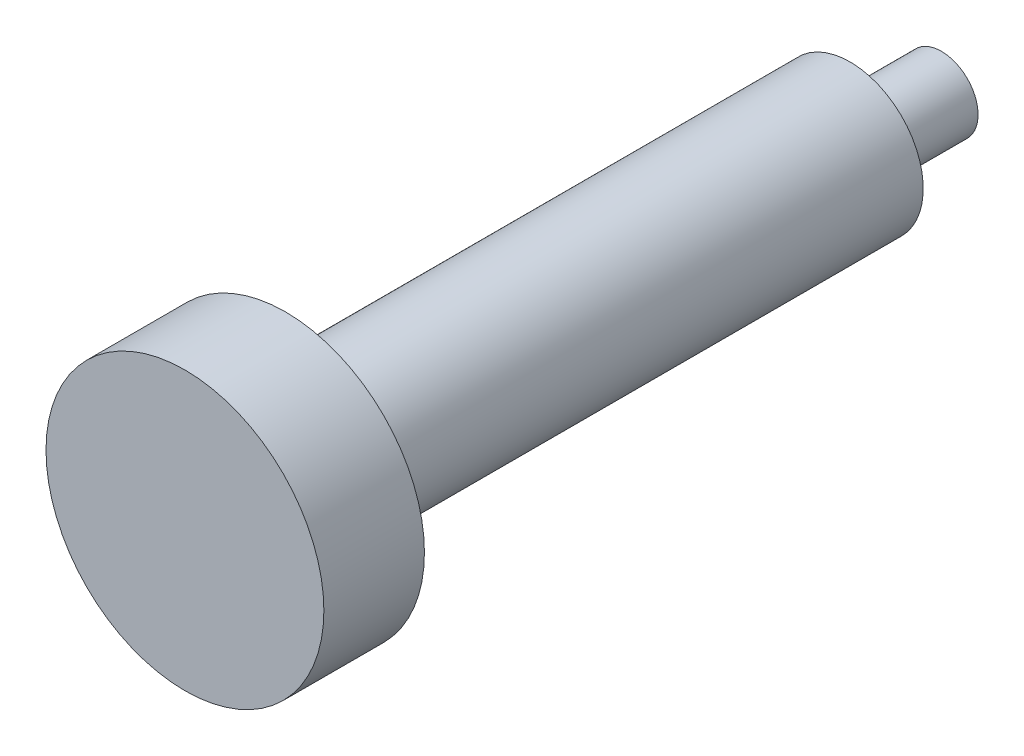
SolidWorks part; units mm, degrees
ref_plane "Ebene vorne" through (0, 0, 0) normal (0, 0, 1) x (1, 0, 0)
ref_plane "Ebene oben" through (0, 0, 0) normal (0, 1, 0) x (1, 0, 0)
ref_plane "Ebene rechts" through (0, 0, 0) normal (1, 0, 0) x (0, 0, -1)
curve "Kurve1"
  spline degree 3 poles (15.998, 0.279, 15.125) (15.9956, 0.372, 15.125) (15.9908, 0.5581, 15.125) (15.9788, 0.8371, 15.125) (15.9618, 1.1158, 15.125) (15.9399, 1.3942, 15.125) (15.9124, 1.6722, 15.125) (15.8823, 1.9501, 15.125) (15.8445, 2.2269, 15.125) (15.804, 2.5031, 15.125) (15.7577, 2.7784, 15.125) (15.7069, 3.0532, 15.125) (15.6507, 3.3268, 15.125) (15.5907, 3.5995, 15.125) (15.5259, 3.871, 15.125) (15.4558, 4.1413, 15.125) (15.3805, 4.4102, 15.125) (15.302, 4.6781, 15.125) (15.2177, 4.9445, 15.125) (15.1287, 5.209, 15.125) (15.0358, 5.4726, 15.125) (14.9376, 5.7341, 15.125) (14.836, 5.9944, 15.125) (14.7286, 6.2521, 15.125) (14.6179, 6.5085, 15.125) (14.5016, 6.7622, 15.125) (14.3819, 7.0146, 15.1251) (14.2566, 7.2643, 15.1247) (14.1278, 7.5122, 15.126) (13.9949, 7.7575, 15.1214) (13.8551, 8.0023, 15.1384) (13.7158, 8.2418, 15.0743) (13.5715, 8.4766, 15.0145) (13.4119, 8.7261, 15.0185) (13.2668, 8.9464, 14.8681) (13.1064, 9.1771, 14.7547) (12.936, 9.4181, 14.6379) (12.7787, 9.6289, 14.4401) (12.5998, 9.8636, 14.2514) (12.4267, 10.0781, 13.9999) (12.2726, 10.2687, 13.7104) (12.058, 10.5174, 13.4954) (11.9048, 10.6904, 13.1908) (11.6957, 10.9206, 12.9578) (11.5109, 11.1135, 12.6897) (11.3198, 11.3099, 12.4304) (11.1162, 11.5085, 12.1963) (10.9182, 11.6978, 11.969) (10.7057, 11.8912, 11.7712) (10.4991, 12.0738, 11.5699) (10.2899, 12.2548, 11.3786) (10.0702, 12.4333, 11.2113) (9.856, 12.6056, 11.046) (9.6251, 12.7816, 10.9139) (9.4039, 12.9462, 10.7491) (9.1806, 13.1038, 10.5834) (8.9611, 13.2571, 10.4164) (8.706, 13.4249, 10.3831) (8.4885, 13.564, 10.2365) (8.2385, 13.7179, 10.2093) (8.0015, 13.8555, 10.1253) (7.7559, 13.9958, 10.0697) (7.5146, 14.1265, 9.9855) (7.2658, 14.2558, 9.9304) (7.0136, 14.3823, 9.9041) (6.7627, 14.5013, 9.853) (6.509, 14.6177, 9.8142) (6.2527, 14.7284, 9.7808) (5.9938, 14.8362, 9.7728) (5.7346, 14.9374, 9.7179) (5.4729, 15.0357, 9.7656) (5.2088, 15.1288, 9.7494) (4.9445, 15.2177, 9.7668) (4.6756, 15.3028, 9.7735) (4.4132, 15.3797, 9.8501) (4.138, 15.4568, 9.8352) (3.8719, 15.5257, 9.9101) (3.5994, 15.5908, 9.9547) (3.3222, 15.6517, 10.0015) (3.0574, 15.7061, 10.1036) (2.7769, 15.758, 10.1515) (2.4995, 15.8045, 10.2212) (2.2248, 15.8448, 10.3192) (1.9478, 15.8826, 10.4276) (1.6757, 15.9121, 10.5538) (1.3922, 15.9401, 10.6531) (1.1115, 15.9621, 10.7671) (0.8378, 15.9789, 10.9076) (0.5476, 15.9908, 11.0382) (0.2878, 15.9992, 11.2279) (-0.0159, 16.0003, 11.3649) (-0.2625, 15.9997, 11.5869) (-0.586, 15.9894, 11.7221) (-0.8156, 15.98, 11.9867) (-1.1413, 15.9601, 12.1562) (-1.3812, 15.941, 12.4304) (-1.6762, 15.9121, 12.6534) (-1.9564, 15.8814, 12.8946) (-2.2189, 15.8456, 13.1573) (-2.5164, 15.8019, 13.3938) (-2.7761, 15.7581, 13.6775) (-3.0552, 15.7065, 13.9546) (-3.3276, 15.6505, 14.2408) (-3.6042, 15.5896, 14.5305) (-3.8666, 15.527, 14.8358) (-4.15, 15.4535, 15.1301) (-4.4027, 15.3826, 15.4504) (-4.6815, 15.301, 15.7484) (-4.9388, 15.2196, 16.0556) (-5.2143, 15.1269, 16.3448) (-5.4717, 15.0361, 16.6509) (-5.7331, 14.938, 16.9543) (-5.9942, 14.836, 17.2552) (-6.2531, 14.7281, 17.554) (-6.5023, 14.6207, 17.855) (-6.7639, 14.5007, 18.1312) (-6.9996, 14.3892, 18.4135) (-7.282, 14.2476, 18.6348) (-7.493, 14.138, 18.9244) (-7.766, 13.9903, 19.1354) (-7.9927, 13.8605, 19.3819) (-8.2391, 13.7175, 19.5942) (-8.476, 13.5718, 19.7935) (-8.7049, 13.4256, 19.9804) (-8.948, 13.2658, 20.1081) (-9.1746, 13.108, 20.2416) (-9.4022, 12.9475, 20.3582) (-9.6265, 12.7805, 20.4464) (-9.8488, 12.6112, 20.5201) (-10.0695, 12.4339, 20.501) (-10.2859, 12.2581, 20.5059) (-10.4973, 12.0754, 20.5054) (-10.7062, 11.8906, 20.5024) (-10.9142, 11.7015, 20.5151) (-11.1162, 11.5085, 20.4665) (-11.3163, 11.3133, 20.4075) (-11.5136, 11.1109, 20.3296) (-11.7057, 10.9097, 20.213) (-11.8883, 10.7089, 20.0701) (-12.0862, 10.4851, 19.9536) (-12.2576, 10.2864, 19.7502) (-12.4416, 10.06, 19.5571) (-12.6114, 9.8485, 19.3123) (-12.7811, 9.6258, 19.0534) (-12.9509, 9.3975, 18.7743) (-13.0975, 9.1894, 18.4671) (-13.2627, 8.9528, 18.2048) (-13.4265, 8.7036, 17.9675) (-13.5612, 8.4929, 17.6888) (-13.7144, 8.2445, 17.4654) (-13.8596, 7.9945, 17.2566) (-13.992, 7.7627, 17.0245) (-14.1253, 7.517, 16.8138) (-14.2569, 7.2636, 16.6283) (-14.3764, 7.0258, 16.4334) (-14.5034, 6.7583, 16.3047) (-14.6163, 6.5122, 16.1473) (-14.7275, 6.2547, 16.0139) (-14.8353, 5.9959, 15.8943) (-14.9368, 5.7363, 15.7837) (-15.0346, 5.4759, 15.6862) (-15.1284, 5.21, 15.6171) (-15.2193, 4.9397, 15.5658) (-15.2997, 4.6858, 15.4471) (-15.3813, 4.4076, 15.4409) (-15.4551, 4.1439, 15.3692) (-15.5264, 3.8691, 15.3634) (-15.5905, 3.6005, 15.3066) (-15.6506, 3.3275, 15.2711) (-15.707, 3.0528, 15.2592) (-15.7576, 2.7791, 15.2222) (-15.804, 2.503, 15.2321) (-15.8445, 2.227, 15.2294) (-15.8823, 1.9501, 15.2301) (-15.9124, 1.6722, 15.23) (-15.9399, 1.3942, 15.23) (-15.9618, 1.1158, 15.23) (-15.9789, 0.8371, 15.23) (-15.9904, 0.5581, 15.23) (-15.9993, 0.2791, 15.23) (-16.0003, 0, 15.23) (-15.9993, -0.2791, 15.23) (-15.9904, -0.5581, 15.23) (-15.9789, -0.8371, 15.23) (-15.9618, -1.1158, 15.23) (-15.9399, -1.3942, 15.23) (-15.9124, -1.6722, 15.23) (-15.8823, -1.9501, 15.23) (-15.8445, -2.2269, 15.23) (-15.804, -2.5031, 15.23) (-15.7577, -2.7784, 15.23) (-15.7069, -3.0532, 15.23) (-15.6507, -3.3268, 15.23) (-15.5907, -3.5995, 15.23) (-15.5259, -3.871, 15.23) (-15.4558, -4.1413, 15.23) (-15.3805, -4.4102, 15.23) (-15.302, -4.6781, 15.23) (-15.2177, -4.9445, 15.23) (-15.1287, -5.209, 15.23) (-15.0358, -5.4726, 15.23) (-14.9376, -5.7341, 15.23) (-14.836, -5.9944, 15.23) (-14.7286, -6.2521, 15.23) (-14.6179, -6.5085, 15.23) (-14.5016, -6.7622, 15.23) (-14.3819, -7.0146, 15.23) (-14.2566, -7.2643, 15.23) (-14.1278, -7.5121, 15.23) (-13.9948, -7.7577, 15.23) (-13.8563, -8.0001, 15.23) (-13.716, -8.2416, 15.23) (-13.5698, -8.4793, 15.23) (-13.4194, -8.7145, 15.23) (-13.266, -8.9478, 15.23) (-13.1062, -9.1772, 15.23) (-12.9451, -9.4055, 15.23) (-12.7782, -9.6295, 15.23) (-12.6091, -9.8516, 15.23) (-12.4341, -10.0692, 15.23) (-12.258, -10.2859, 15.23) (-12.0755, -10.4973, 15.23) (-11.8905, -10.7064, 15.23) (-11.7026, -10.9131, 15.23) (-11.5097, -11.115, 15.23) (-11.3148, -11.3148, 15.23) (-11.115, -11.5097, 15.23) (-10.9131, -11.7026, 15.23) (-10.7064, -11.8905, 15.23) (-10.4973, -12.0755, 15.23) (-10.2859, -12.258, 15.23) (-10.0692, -12.4341, 15.23) (-9.8516, -12.6091, 15.23) (-9.6295, -12.7782, 15.23) (-9.4055, -12.9451, 15.23) (-9.1772, -13.1062, 15.23) (-8.9478, -13.266, 15.23) (-8.7145, -13.4194, 15.23) (-8.4793, -13.5698, 15.23) (-8.2416, -13.716, 15.23) (-8.0001, -13.8563, 15.23) (-7.7577, -13.9948, 15.23) (-7.5121, -14.1278, 15.23) (-7.2643, -14.2566, 15.23) (-7.0146, -14.3819, 15.23) (-6.7622, -14.5016, 15.23) (-6.5085, -14.6179, 15.23) (-6.2521, -14.7286, 15.23) (-5.9944, -14.836, 15.23) (-5.7341, -14.9376, 15.23) (-5.4726, -15.0358, 15.23) (-5.209, -15.1287, 15.23) (-4.9445, -15.2177, 15.23) (-4.6781, -15.302, 15.23) (-4.4102, -15.3805, 15.23) (-4.1413, -15.4558, 15.23) (-3.871, -15.5259, 15.23) (-3.5995, -15.5907, 15.23) (-3.3268, -15.6507, 15.23) (-3.0532, -15.7069, 15.23) (-2.7784, -15.7577, 15.23) (-2.5031, -15.804, 15.23) (-2.2269, -15.8445, 15.23) (-1.9501, -15.8823, 15.23) (-1.6722, -15.9124, 15.23) (-1.3942, -15.9399, 15.23) (-1.1158, -15.9618, 15.23) (-0.8371, -15.9789, 15.23) (-0.5581, -15.9904, 15.23) (-0.2791, -15.9993, 15.23) (0, -16.0003, 15.23) (0.2791, -15.9993, 15.23) (0.5581, -15.9904, 15.23) (0.8371, -15.9789, 15.23) (1.1158, -15.9618, 15.23) (1.3942, -15.9399, 15.23) (1.6722, -15.9124, 15.23) (1.9501, -15.8823, 15.23) (2.2269, -15.8445, 15.23) (2.5031, -15.804, 15.23) (2.7784, -15.7577, 15.23) (3.0532, -15.7069, 15.23) (3.3268, -15.6507, 15.23) (3.5995, -15.5907, 15.23) (3.871, -15.5259, 15.23) (4.1413, -15.4558, 15.23) (4.4102, -15.3805, 15.23) (4.6781, -15.302, 15.23) (4.9445, -15.2177, 15.23) (5.209, -15.1287, 15.23) (5.4726, -15.0358, 15.23) (5.7341, -14.9376, 15.23) (5.9944, -14.836, 15.23) (6.2521, -14.7286, 15.23) (6.5085, -14.6179, 15.23) (6.7622, -14.5016, 15.23) (7.0146, -14.3819, 15.23) (7.2643, -14.2566, 15.23) (7.5121, -14.1278, 15.23) (7.7577, -13.9948, 15.23) (8.0001, -13.8563, 15.23) (8.2416, -13.716, 15.23) (8.4793, -13.5698, 15.23) (8.7145, -13.4194, 15.23) (8.9478, -13.266, 15.23) (9.1772, -13.1062, 15.23) (9.4055, -12.9451, 15.23) (9.6295, -12.7782, 15.23) (9.8516, -12.6091, 15.23) (10.0692, -12.4341, 15.23) (10.2859, -12.258, 15.23) (10.4973, -12.0755, 15.23) (10.7064, -11.8905, 15.23) (10.9131, -11.7026, 15.23) (11.115, -11.5097, 15.23) (11.3148, -11.3148, 15.23) (11.5097, -11.115, 15.23) (11.7025, -10.9131, 15.23) (11.8906, -10.7065, 15.23) (12.0135, -10.5668, 15.23) (12.075, -10.497, 15.23) knots 0 0 0 0 0.002912 0.005826 0.008742 0.011651 0.014566 0.017484 0.0204 0.023311 0.02622 0.029138 0.032056 0.034962 0.03788 0.04079 0.043703 0.046618 0.049529 0.052445 0.055356 0.058274 0.061188 0.064102 0.067014 0.069927 0.072839 0.075755 0.078672 0.08158 0.084496 0.087455 0.090415 0.09334 0.096512 0.099686 0.102883 0.106374 0.10993 0.113838 0.118001 0.121744 0.125981 0.12982 0.133843 0.137819 0.141622 0.14537 0.148951 0.152534 0.156059 0.15947 0.162825 0.166087 0.169441 0.172856 0.176142 0.179146 0.182273 0.185242 0.188246 0.191239 0.194251 0.197223 0.200162 0.203112 0.206055 0.208983 0.211905 0.214835 0.217761 0.220672 0.22359 0.226508 0.22947 0.232387 0.235353 0.238318 0.24128 0.244329 0.247314 0.250313 0.253388 0.256522 0.259697 0.262811 0.265958 0.269197 0.272456 0.275893 0.279223 0.282804 0.286161 0.290003 0.293529 0.297507 0.301282 0.305127 0.30911 0.31295 0.317072 0.321202 0.325367 0.329563 0.33388 0.338116 0.342547 0.346824 0.351137 0.355339 0.359652 0.363969 0.368246 0.372522 0.376797 0.380923 0.385011 0.388787 0.392915 0.39662 0.400464 0.40414 0.407724 0.411186 0.414423 0.41764 0.420795 0.423852 0.426835 0.429745 0.432659 0.435574 0.438486 0.441396 0.444348 0.447322 0.450346 0.453505 0.456738 0.45995 0.463475 0.467059 0.470898 0.474882 0.479004 0.483361 0.487344 0.491186 0.495272 0.499013 0.502658 0.506434 0.510076 0.513602 0.517099 0.520357 0.523664 0.526898 0.53007 0.533202 0.536284 0.539285 0.542279 0.545337 0.548275 0.551235 0.554157 0.557112 0.560041 0.562966 0.565896 0.568805 0.571716 0.574632 0.57755 0.580464 0.583374 0.58629 0.589204 0.592116 0.595027 0.597938 0.60085 0.603764 0.60668 0.609589 0.612503 0.615422 0.618338 0.621249 0.624158 0.627076 0.629994 0.6329 0.635818 0.638728 0.641641 0.644556 0.647467 0.650383 0.653294 0.656212 0.659126 0.66204 0.664951 0.667865 0.670777 0.673693 0.67661 0.679518 0.682434 0.685347 0.68826 0.691169 0.694083 0.697 0.699918 0.702827 0.705744 0.708654 0.711568 0.714483 0.717395 0.720305 0.723227 0.726134 0.729041 0.731964 0.734873 0.737785 0.7407 0.743614 0.746524 0.749442 0.75235 0.755268 0.758186 0.7611 0.764008 0.766922 0.769835 0.77275 0.775659 0.778575 0.781492 0.784404 0.787317 0.790228 0.793142 0.796056 0.798975 0.801885 0.804802 0.807712 0.810627 0.813541 0.816451 0.819369 0.822275 0.825193 0.828111 0.83102 0.833931 0.836847 0.839765 0.842679 0.845589 0.848505 0.851418 0.854331 0.857242 0.860153 0.863065 0.865978 0.868894 0.871804 0.874718 0.877637 0.880552 0.883463 0.886372 0.889291 0.892208 0.895114 0.898032 0.900942 0.903856 0.906771 0.909681 0.912598 0.915508 0.918427 0.921341 0.924255 0.927166 0.930079 0.932992 0.935908 0.938824 0.941733 0.944648 0.947562 0.950475 0.953383 0.956297 0.959215 0.962133 0.965042 0.967959 0.970869 0.973783 0.976698 0.97961 0.98252 0.985442 0.988349 0.991256 0.994178 0.997088 1 1 1 1
curve "Kurve2"
  spline degree 3 poles (15.998, 0.279, 58.63) (15.9956, 0.372, 58.63) (15.9908, 0.5581, 58.63) (15.9788, 0.8371, 58.63) (15.9618, 1.1158, 58.63) (15.9399, 1.3942, 58.63) (15.9124, 1.6722, 58.63) (15.8823, 1.9501, 58.63) (15.8445, 2.2269, 58.63) (15.804, 2.5031, 58.63) (15.7577, 2.7784, 58.63) (15.7069, 3.0532, 58.63) (15.6507, 3.3268, 58.63) (15.5907, 3.5995, 58.63) (15.5259, 3.871, 58.63) (15.4558, 4.1413, 58.63) (15.3805, 4.4102, 58.63) (15.302, 4.6781, 58.63) (15.2177, 4.9445, 58.63) (15.1287, 5.209, 58.63) (15.0358, 5.4726, 58.63) (14.9376, 5.7341, 58.63) (14.836, 5.9944, 58.63) (14.7286, 6.2521, 58.63) (14.6179, 6.5085, 58.63) (14.5016, 6.7622, 58.63) (14.3819, 7.0146, 58.63) (14.2566, 7.2643, 58.63) (14.1278, 7.5121, 58.63) (13.9948, 7.7577, 58.63) (13.8563, 8.0001, 58.63) (13.716, 8.2416, 58.63) (13.5698, 8.4793, 58.63) (13.4194, 8.7145, 58.63) (13.266, 8.9478, 58.63) (13.1062, 9.1772, 58.63) (12.9451, 9.4055, 58.63) (12.7782, 9.6295, 58.63) (12.6091, 9.8516, 58.63) (12.4341, 10.0692, 58.63) (12.258, 10.2859, 58.63) (12.0755, 10.4973, 58.63) (11.8905, 10.7064, 58.63) (11.7026, 10.9131, 58.63) (11.5097, 11.115, 58.63) (11.3148, 11.3148, 58.63) (11.115, 11.5097, 58.63) (10.9131, 11.7026, 58.63) (10.7064, 11.8905, 58.63) (10.4973, 12.0755, 58.63) (10.2859, 12.258, 58.63) (10.0692, 12.4341, 58.63) (9.8516, 12.6091, 58.63) (9.6295, 12.7782, 58.63) (9.4055, 12.9451, 58.63) (9.1772, 13.1062, 58.63) (8.9478, 13.266, 58.63) (8.7145, 13.4194, 58.63) (8.4793, 13.5698, 58.63) (8.2416, 13.716, 58.63) (8.0001, 13.8563, 58.63) (7.7577, 13.9948, 58.63) (7.5121, 14.1278, 58.63) (7.2643, 14.2566, 58.63) (7.0146, 14.3819, 58.63) (6.7622, 14.5016, 58.63) (6.5085, 14.6179, 58.63) (6.2521, 14.7286, 58.63) (5.9944, 14.836, 58.63) (5.7341, 14.9376, 58.63) (5.4726, 15.0358, 58.63) (5.209, 15.1287, 58.63) (4.9445, 15.2177, 58.63) (4.6781, 15.302, 58.63) (4.4102, 15.3805, 58.63) (4.1413, 15.4558, 58.63) (3.871, 15.5259, 58.63) (3.5995, 15.5907, 58.63) (3.3268, 15.6507, 58.63) (3.0532, 15.7069, 58.63) (2.7784, 15.7577, 58.63) (2.5031, 15.804, 58.63) (2.2269, 15.8445, 58.63) (1.9501, 15.8823, 58.63) (1.6722, 15.9124, 58.63) (1.3942, 15.9399, 58.63) (1.1158, 15.9618, 58.63) (0.8371, 15.9789, 58.63) (0.5581, 15.9904, 58.63) (0.2791, 15.9993, 58.63) (0, 16.0003, 58.63) (-0.2791, 15.9993, 58.63) (-0.5581, 15.9904, 58.63) (-0.8371, 15.9789, 58.63) (-1.1158, 15.9618, 58.63) (-1.3942, 15.9399, 58.63) (-1.6722, 15.9124, 58.63) (-1.9501, 15.8823, 58.63) (-2.2269, 15.8445, 58.63) (-2.5031, 15.804, 58.63) (-2.7784, 15.7577, 58.63) (-3.0532, 15.7069, 58.63) (-3.3268, 15.6507, 58.63) (-3.5995, 15.5907, 58.63) (-3.871, 15.5259, 58.63) (-4.1413, 15.4558, 58.63) (-4.4102, 15.3805, 58.63) (-4.6781, 15.302, 58.63) (-4.9445, 15.2177, 58.63) (-5.209, 15.1287, 58.63) (-5.4726, 15.0358, 58.63) (-5.7341, 14.9376, 58.63) (-5.9944, 14.836, 58.63) (-6.2521, 14.7286, 58.63) (-6.5085, 14.6179, 58.63) (-6.7622, 14.5016, 58.63) (-7.0146, 14.3819, 58.63) (-7.2643, 14.2566, 58.63) (-7.5121, 14.1278, 58.63) (-7.7577, 13.9948, 58.63) (-8.0001, 13.8563, 58.63) (-8.2416, 13.716, 58.63) (-8.4793, 13.5698, 58.63) (-8.7145, 13.4194, 58.63) (-8.9478, 13.266, 58.63) (-9.1772, 13.1062, 58.63) (-9.4055, 12.9451, 58.63) (-9.6295, 12.7782, 58.63) (-9.8516, 12.6091, 58.63) (-10.0692, 12.4341, 58.63) (-10.2859, 12.258, 58.63) (-10.4973, 12.0755, 58.63) (-10.7064, 11.8905, 58.63) (-10.9131, 11.7026, 58.63) (-11.115, 11.5097, 58.63) (-11.3148, 11.3148, 58.63) (-11.5097, 11.115, 58.63) (-11.7026, 10.9131, 58.63) (-11.8905, 10.7064, 58.63) (-12.0755, 10.4973, 58.63) (-12.258, 10.2859, 58.63) (-12.4341, 10.0692, 58.63) (-12.6091, 9.8516, 58.63) (-12.7782, 9.6295, 58.63) (-12.9451, 9.4055, 58.63) (-13.1062, 9.1772, 58.63) (-13.266, 8.9478, 58.63) (-13.4194, 8.7145, 58.63) (-13.5698, 8.4793, 58.63) (-13.716, 8.2416, 58.63) (-13.8563, 8.0001, 58.63) (-13.9948, 7.7577, 58.63) (-14.1278, 7.5121, 58.63) (-14.2566, 7.2643, 58.63) (-14.3819, 7.0146, 58.63) (-14.5016, 6.7622, 58.63) (-14.6179, 6.5085, 58.63) (-14.7286, 6.2521, 58.63) (-14.836, 5.9944, 58.63) (-14.9376, 5.7341, 58.63) (-15.0358, 5.4726, 58.63) (-15.1287, 5.209, 58.63) (-15.2177, 4.9445, 58.63) (-15.302, 4.6781, 58.63) (-15.3805, 4.4102, 58.63) (-15.4558, 4.1413, 58.63) (-15.5259, 3.871, 58.63) (-15.5907, 3.5995, 58.63) (-15.6507, 3.3268, 58.63) (-15.7069, 3.0532, 58.63) (-15.7577, 2.7784, 58.63) (-15.804, 2.5031, 58.63) (-15.8445, 2.2269, 58.63) (-15.8823, 1.9501, 58.63) (-15.9124, 1.6722, 58.63) (-15.9399, 1.3942, 58.63) (-15.9618, 1.1158, 58.63) (-15.9789, 0.8371, 58.63) (-15.9904, 0.5581, 58.63) (-15.9993, 0.2791, 58.63) (-16.0003, 0, 58.63) (-15.9993, -0.2791, 58.63) (-15.9904, -0.5581, 58.63) (-15.9789, -0.8371, 58.63) (-15.9618, -1.1158, 58.63) (-15.9399, -1.3942, 58.63) (-15.9124, -1.6722, 58.63) (-15.8823, -1.9501, 58.63) (-15.8445, -2.2269, 58.63) (-15.804, -2.5031, 58.63) (-15.7577, -2.7784, 58.63) (-15.7069, -3.0532, 58.63) (-15.6507, -3.3268, 58.63) (-15.5907, -3.5995, 58.63) (-15.5259, -3.871, 58.63) (-15.4558, -4.1413, 58.63) (-15.3805, -4.4102, 58.63) (-15.302, -4.6781, 58.63) (-15.2177, -4.9445, 58.63) (-15.1287, -5.209, 58.63) (-15.0358, -5.4726, 58.63) (-14.9376, -5.7341, 58.63) (-14.836, -5.9944, 58.63) (-14.7286, -6.2521, 58.63) (-14.6179, -6.5085, 58.6301) (-14.5016, -6.7622, 58.6298) (-14.3818, -7.0146, 58.6308) (-14.2567, -7.2641, 58.6271) (-14.1271, -7.5136, 58.6407) (-13.9945, -7.7583, 58.5895) (-13.8563, -8.0002, 58.5403) (-13.716, -8.2417, 58.489) (-13.5647, -8.4873, 58.4419) (-13.4193, -8.7147, 58.3115) (-13.2626, -8.9527, 58.194) (-13.1041, -9.1802, 58.0385) (-12.9343, -9.4203, 57.8699) (-12.7843, -9.6214, 57.624) (-12.6003, -9.8629, 57.4189) (-12.4377, -10.0647, 57.1567) (-12.2556, -10.2889, 56.9178) (-12.0823, -10.4894, 56.6626) (-11.8847, -10.7129, 56.4471) (-11.7036, -10.9118, 56.1999) (-11.5164, -11.1081, 55.958) (-11.3069, -11.3227, 55.7538) (-11.1226, -11.5023, 55.5069) (-10.9138, -11.702, 55.3019) (-10.709, -11.8881, 55.1001) (-10.5017, -12.0717, 54.9123) (-10.2819, -12.2614, 54.7535) (-10.0735, -12.4306, 54.5678) (-9.855, -12.6065, 54.4085) (-9.6301, -12.7778, 54.27) (-9.4058, -12.9449, 54.1359) (-9.1816, -13.1032, 53.9993) (-8.9418, -13.27, 53.9032) (-8.7215, -13.4148, 53.752) (-8.4799, -13.5694, 53.6608) (-8.2429, -13.7152, 53.5686) (-8.0014, -13.8556, 53.4875) (-7.7571, -13.9951, 53.4233) (-7.5155, -14.1261, 53.3405) (-7.2628, -14.2573, 53.3169) (-7.0166, -14.3809, 53.2517) (-6.7618, -14.5018, 53.2374) (-6.5081, -14.6181, 53.2088) (-6.2535, -14.728, 53.1574) (-5.9935, -14.8363, 53.1816) (-5.7349, -14.9373, 53.1359) (-5.4723, -15.0359, 53.1449) (-5.2083, -15.1289, 53.1543) (-4.9454, -15.2174, 53.198) (-4.6773, -15.3023, 53.1933) (-4.4095, -15.3807, 53.2289) (-4.1416, -15.4558, 53.2715) (-3.8693, -15.5263, 53.3051) (-3.6007, -15.5905, 53.3693) (-3.3233, -15.6514, 53.4076) (-3.0544, -15.7067, 53.4935) (-2.7776, -15.7579, 53.5583) (-2.5017, -15.8042, 53.6335) (-2.2259, -15.8446, 53.7198) (-1.9453, -15.8829, 53.8109) (-1.6719, -15.9124, 53.9346) (-1.3988, -15.9396, 54.0608) (-1.1033, -15.9627, 54.1494) (-0.8425, -15.9786, 54.3208) (-0.5566, -15.9905, 54.4536) (-0.2731, -15.9994, 54.5979) (0.002, -16.0003, 54.7702) (0.2797, -15.9993, 54.9506) (0.5635, -15.9902, 55.1339) (0.8388, -15.9789, 55.3411) (1.1194, -15.9615, 55.5538) (1.3909, -15.9402, 55.7825) (1.6827, -15.9113, 55.9974) (1.9411, -15.8834, 56.2538) (2.243, -15.8423, 56.4787) (2.5036, -15.8038, 56.7613) (2.7688, -15.7594, 57.0451) (3.0614, -15.7054, 57.3011) (3.3403, -15.6477, 57.5858) (3.5798, -15.5953, 57.9107) (3.8868, -15.5221, 58.1794) (4.141, -15.4558, 58.4971) (4.4045, -15.3822, 58.8136) (4.6803, -15.3013, 59.1146) (4.9442, -15.2178, 59.4202) (5.2065, -15.1295, 59.7241) (5.4722, -15.036, 60.0204) (5.7373, -14.9364, 60.3151) (5.9924, -14.8368, 60.6204) (6.2532, -14.7281, 60.9189) (6.5027, -14.6205, 61.2194) (6.7629, -14.5013, 61.4993) (7.013, -14.3826, 61.7783) (7.2537, -14.262, 62.0501) (7.5133, -14.1273, 62.2785) (7.7587, -13.9942, 62.5102) (7.9979, -13.8576, 62.7446) (8.2381, -13.7181, 62.9703) (8.4782, -13.5704, 63.1782) (8.7074, -13.424, 63.3829) (8.9474, -13.2663, 63.5474) (9.1687, -13.1121, 63.7156) (9.4029, -12.947, 63.8279) (9.6312, -12.777, 63.9146) (9.8458, -12.6136, 64.0332) (10.0728, -12.4312, 64.0659) (10.2802, -12.2628, 64.1843) (10.498, -12.0749, 64.1536) (10.7062, -11.8907, 64.1617) (10.9131, -11.7025, 64.1595) (11.115, -11.5097, 64.1601) (11.3148, -11.3148, 64.16) (11.5097, -11.115, 64.16) (11.7026, -10.9131, 64.16) (11.8904, -10.7063, 64.16) (12.0758, -10.4975, 64.16) (12.1966, -10.3559, 64.16) (12.257, -10.285, 64.16) knots 0 0 0 0 0.002952 0.005906 0.008862 0.011811 0.014765 0.017724 0.02068 0.023631 0.02658 0.029538 0.032496 0.035442 0.038399 0.041349 0.044303 0.047258 0.050208 0.053165 0.056115 0.059074 0.062028 0.064982 0.067933 0.070886 0.073838 0.076795 0.079751 0.0827 0.085655 0.088608 0.091561 0.09451 0.097464 0.100421 0.103379 0.106328 0.109286 0.112236 0.115189 0.118144 0.121096 0.124046 0.127009 0.129955 0.132902 0.135865 0.138814 0.141766 0.144721 0.147675 0.150625 0.153582 0.156531 0.159489 0.162447 0.1654 0.168349 0.171302 0.174255 0.177211 0.180159 0.183116 0.186072 0.189024 0.191977 0.194929 0.197883 0.200837 0.203795 0.206746 0.209702 0.212652 0.215607 0.218561 0.221511 0.224469 0.227415 0.230373 0.233331 0.23628 0.239231 0.242187 0.245145 0.248099 0.251049 0.254005 0.256958 0.259911 0.262861 0.265812 0.268764 0.271718 0.274674 0.277624 0.280578 0.283536 0.286492 0.289443 0.292392 0.29535 0.298308 0.301254 0.304212 0.307162 0.310115 0.31307 0.316021 0.318977 0.321928 0.324886 0.32784 0.330794 0.333745 0.336699 0.339651 0.342607 0.345564 0.348512 0.351468 0.354421 0.357374 0.360322 0.363276 0.366234 0.369192 0.372141 0.375098 0.378048 0.381002 0.383957 0.386909 0.389858 0.392821 0.395768 0.398714 0.401677 0.404627 0.407579 0.410534 0.413487 0.416437 0.419395 0.422343 0.425302 0.428259 0.431213 0.434161 0.437115 0.440068 0.443023 0.445972 0.448928 0.451884 0.454837 0.45779 0.460741 0.463695 0.466649 0.469607 0.472558 0.475514 0.478465 0.48142 0.484373 0.487323 0.490281 0.493227 0.496185 0.499143 0.502092 0.505043 0.507999 0.510957 0.513912 0.516861 0.519817 0.522771 0.525723 0.528674 0.531625 0.534577 0.53753 0.540487 0.543436 0.54639 0.549349 0.552304 0.555255 0.558204 0.561163 0.56412 0.567066 0.570024 0.572974 0.575928 0.578883 0.581833 0.58479 0.58774 0.590699 0.593653 0.596607 0.599558 0.602511 0.605463 0.608419 0.611376 0.614355 0.617357 0.620357 0.623378 0.626567 0.629804 0.63316 0.636649 0.640506 0.644236 0.648233 0.652162 0.656128 0.659886 0.663813 0.667714 0.671404 0.675293 0.678996 0.682626 0.686167 0.689599 0.693113 0.696514 0.699821 0.703098 0.70636 0.709538 0.712818 0.715951 0.719054 0.722126 0.725173 0.728213 0.731199 0.734202 0.737166 0.740137 0.743111 0.746065 0.749031 0.751989 0.754944 0.757917 0.76087 0.763842 0.766825 0.769806 0.77282 0.775813 0.778876 0.781925 0.784979 0.788064 0.791185 0.794405 0.79762 0.800771 0.804152 0.807456 0.810782 0.814238 0.81775 0.821291 0.824955 0.828685 0.832475 0.836235 0.840203 0.844031 0.848212 0.852429 0.856432 0.860655 0.865182 0.869293 0.873743 0.878235 0.882571 0.886943 0.891318 0.895613 0.899912 0.904286 0.908621 0.912955 0.917137 0.921318 0.925429 0.929257 0.93308 0.936941 0.940734 0.944429 0.948058 0.951516 0.954923 0.958122 0.961237 0.964378 0.967395 0.970468 0.973423 0.976375 0.979325 0.982287 0.985234 0.988181 0.991143 0.994093 0.997045 1 1 1 1
curve "Kurve3"
  spline degree 3 poles (15.998, 0.279, 106.17) (15.9956, 0.372, 106.17) (15.9908, 0.5581, 106.17) (15.9788, 0.8371, 106.17) (15.9618, 1.1158, 106.17) (15.9399, 1.3942, 106.17) (15.9124, 1.6722, 106.17) (15.8823, 1.9501, 106.17) (15.8445, 2.2269, 106.17) (15.804, 2.5031, 106.1701) (15.7577, 2.7784, 106.1697) (15.7069, 3.0533, 106.1713) (15.6508, 3.3263, 106.1653) (15.5899, 3.6032, 106.1878) (15.5267, 3.8681, 106.1022) (15.4544, 4.1469, 106.0941) (15.3803, 4.4108, 105.9973) (15.3012, 4.6807, 105.9132) (15.217, 4.9466, 105.8055) (15.1268, 5.2145, 105.6875) (15.0323, 5.4822, 105.5382) (14.9387, 5.7313, 105.3421) (14.834, 5.9994, 105.1612) (14.7257, 6.2587, 104.9557) (14.62, 6.5039, 104.7237) (14.5017, 6.762, 104.5097) (14.3788, 7.0207, 104.2969) (14.2603, 7.2571, 104.0566) (14.1218, 7.5236, 103.8472) (13.9948, 7.7575, 103.5898) (13.8628, 7.989, 103.333) (13.7112, 8.2497, 103.1232) (13.5722, 8.4753, 102.8777) (13.4177, 8.717, 102.652) (13.2708, 8.9406, 102.4142) (13.11, 9.1718, 102.2103) (12.9485, 9.4009, 102.032) (12.7734, 9.6359, 101.8851) (12.6138, 9.8455, 101.6956) (12.4335, 10.0701, 101.5464) (12.2595, 10.2841, 101.3918) (12.0833, 10.4884, 101.2377) (11.8872, 10.7101, 101.1752) (11.708, 10.9072, 101.0512) (11.5084, 11.1163, 101.0162) (11.3162, 11.3134, 100.9447) (11.1153, 11.5094, 100.9063) (10.9141, 11.7016, 100.8602) (10.7059, 11.891, 100.8732) (10.4977, 12.0751, 100.8367) (10.2858, 12.2582, 100.8498) (10.0693, 12.4341, 100.8339) (9.8516, 12.6091, 100.8246) (9.6294, 12.7783, 100.8175) (9.4057, 12.945, 100.7953) (9.1772, 13.1062, 100.8013) (8.9478, 13.266, 100.7997) (8.7145, 13.4194, 100.8001) (8.4793, 13.5698, 100.8) (8.2416, 13.716, 100.8) (8.0001, 13.8563, 100.8) (7.7577, 13.9948, 100.8) (7.5121, 14.1278, 100.8) (7.2643, 14.2566, 100.8) (7.0146, 14.3819, 100.8) (6.7622, 14.5016, 100.8) (6.5085, 14.6179, 100.8) (6.2521, 14.7286, 100.8) (5.9944, 14.836, 100.8) (5.7341, 14.9376, 100.8) (5.4726, 15.0358, 100.8) (5.209, 15.1287, 100.8) (4.9445, 15.2177, 100.8) (4.6781, 15.302, 100.8) (4.4102, 15.3805, 100.8) (4.1413, 15.4558, 100.8) (3.871, 15.5259, 100.8) (3.5995, 15.5907, 100.8) (3.3268, 15.6507, 100.8) (3.0532, 15.7069, 100.8) (2.7784, 15.7577, 100.8) (2.5031, 15.804, 100.8) (2.2269, 15.8445, 100.8) (1.9501, 15.8823, 100.8) (1.6722, 15.9124, 100.8) (1.3942, 15.9399, 100.8) (1.1158, 15.9618, 100.8) (0.8371, 15.9789, 100.8) (0.5581, 15.9904, 100.8) (0.2791, 15.9993, 100.8) (0, 16.0003, 100.8) (-0.2791, 15.9993, 100.8) (-0.5581, 15.9904, 100.8) (-0.8371, 15.9789, 100.8) (-1.1158, 15.9618, 100.8) (-1.3942, 15.9399, 100.8) (-1.6722, 15.9124, 100.8) (-1.9501, 15.8823, 100.8) (-2.2269, 15.8445, 100.8) (-2.5031, 15.804, 100.8) (-2.7784, 15.7577, 100.8) (-3.0532, 15.7069, 100.8) (-3.3268, 15.6507, 100.8) (-3.5995, 15.5907, 100.8) (-3.871, 15.5259, 100.8) (-4.1413, 15.4558, 100.8) (-4.4102, 15.3805, 100.8) (-4.6781, 15.302, 100.8) (-4.9445, 15.2177, 100.8) (-5.209, 15.1287, 100.8) (-5.4726, 15.0358, 100.8) (-5.7341, 14.9376, 100.8) (-5.9944, 14.836, 100.8) (-6.2521, 14.7286, 100.8) (-6.5085, 14.6179, 100.8) (-6.7622, 14.5016, 100.8) (-7.0146, 14.3819, 100.8) (-7.2643, 14.2566, 100.8) (-7.5121, 14.1278, 100.8) (-7.7577, 13.9948, 100.8) (-8.0001, 13.8563, 100.8) (-8.2416, 13.716, 100.8) (-8.4793, 13.5698, 100.8) (-8.7145, 13.4194, 100.8) (-8.9478, 13.266, 100.8) (-9.1772, 13.1062, 100.8) (-9.4055, 12.9451, 100.8) (-9.6295, 12.7782, 100.8) (-9.8516, 12.6091, 100.8) (-10.0692, 12.4341, 100.8) (-10.2859, 12.258, 100.8) (-10.4973, 12.0755, 100.8) (-10.7064, 11.8905, 100.8) (-10.9131, 11.7026, 100.8) (-11.115, 11.5097, 100.8) (-11.3148, 11.3148, 100.8) (-11.5097, 11.115, 100.8) (-11.7026, 10.9131, 100.8) (-11.8905, 10.7064, 100.8) (-12.0755, 10.4973, 100.8) (-12.258, 10.2859, 100.8) (-12.4341, 10.0692, 100.8) (-12.6091, 9.8516, 100.8) (-12.7782, 9.6295, 100.8) (-12.9451, 9.4055, 100.8001) (-13.1062, 9.1772, 100.7997) (-13.266, 8.9477, 100.801) (-13.4193, 8.7147, 100.7964) (-13.5708, 8.4777, 100.8133) (-13.7152, 8.2429, 100.7498) (-13.8564, 8, 100.7477) (-13.9984, 7.7512, 100.7289) (-14.1271, 7.5135, 100.6208) (-14.2558, 7.266, 100.5373) (-14.3841, 7.0099, 100.4712) (-14.5032, 6.7588, 100.3608) (-14.6209, 6.5017, 100.2339) (-14.7287, 6.252, 100.0662) (-14.846, 5.9695, 99.9014) (-14.9319, 5.7488, 99.6279) (-15.0406, 5.4595, 99.4146) (-15.1262, 5.216, 99.1467) (-15.2193, 4.9399, 98.907) (-15.3011, 4.6811, 98.6483) (-15.3818, 4.4058, 98.4017) (-15.4534, 4.1502, 98.1396) (-15.5254, 3.8731, 97.9104) (-15.5909, 3.5987, 97.6912) (-15.6497, 3.3313, 97.4689) (-15.7066, 3.0547, 97.2663) (-15.7567, 2.7841, 97.0679) (-15.8046, 2.4994, 96.8974) (-15.8437, 2.2317, 96.7093) (-15.8815, 1.9575, 96.5395) (-15.9136, 1.6603, 96.4149) (-15.9385, 1.4105, 96.2185) (-15.962, 1.1147, 96.1184) (-15.9787, 0.8401, 96.0026) (-15.9904, 0.5607, 95.9064) (-15.9994, 0.276, 95.835) (-16.0003, 0.0022, 95.7312) (-15.9993, -0.2791, 95.652) (-15.9906, -0.5543, 95.5624) (-15.9788, -0.8392, 95.5213) (-15.962, -1.1127, 95.442) (-15.9399, -1.3947, 95.4128) (-15.9125, -1.6713, 95.3668) (-15.8823, -1.95, 95.3404) (-15.8445, -2.2265, 95.312) (-15.804, -2.5032, 95.3017) (-15.7577, -2.7782, 95.281) (-15.7069, -3.0532, 95.2842) (-15.6507, -3.327, 95.2922) (-15.5907, -3.5998, 95.257) (-15.526, -3.8706, 95.3) (-15.4558, -4.1418, 95.2831) (-15.3794, -4.4141, 95.3081) (-15.3035, -4.6731, 95.4068) (-15.2168, -4.9475, 95.373) (-15.1284, -5.2099, 95.4423) (-15.0349, -5.4749, 95.4999) (-14.9386, -5.7315, 95.5907) (-14.8351, -5.9966, 95.6458) (-14.7278, -6.2541, 95.7285) (-14.6173, -6.51, 95.8238) (-14.501, -6.7634, 95.9299) (-14.3797, -7.0189, 96.041) (-14.2582, -7.2611, 96.1843) (-14.1252, -7.5172, 96.2999) (-13.996, -7.7555, 96.4533) (-13.8541, -8.0041, 96.5877) (-13.7121, -8.248, 96.7482) (-13.5704, -8.4782, 96.9403) (-13.4219, -8.7107, 97.1285) (-13.258, -8.9595, 97.2928) (-13.1164, -9.1627, 97.5245) (-12.9343, -9.4206, 97.6728) (-12.7732, -9.636, 97.9082) (-12.613, -9.8466, 98.1667) (-12.4267, -10.0785, 98.4091) (-12.2616, -10.2816, 98.6908) (-12.0775, -10.4951, 98.955) (-11.8869, -10.7103, 99.2073) (-11.7131, -10.9018, 99.478) (-11.5057, -11.119, 99.6894) (-11.3263, -11.3033, 99.9246) (-11.1163, -11.5085, 100.0886) (-10.9163, -11.6995, 100.247) (-10.7094, -11.8878, 100.3799) (-10.5034, -12.0702, 100.5005) (-10.2856, -12.2584, 100.5474) (-10.0709, -12.4327, 100.6083) (-9.8526, -12.6083, 100.6474) (-9.6259, -12.7809, 100.6116) (-9.409, -12.9425, 100.717) (-9.1767, -13.1066, 100.6891) (-8.9479, -13.2659, 100.6966) (-8.7144, -13.4194, 100.6946) (-8.4793, -13.5697, 100.6951) (-8.2416, -13.716, 100.695) (-8.0001, -13.8563, 100.695) (-7.7577, -13.9948, 100.695) (-7.5121, -14.1278, 100.695) (-7.2643, -14.2566, 100.695) (-7.0146, -14.3819, 100.695) (-6.7622, -14.5016, 100.695) (-6.5085, -14.6179, 100.695) (-6.2521, -14.7286, 100.695) (-5.9944, -14.836, 100.695) (-5.7341, -14.9376, 100.695) (-5.4726, -15.0358, 100.695) (-5.209, -15.1287, 100.695) (-4.9445, -15.2177, 100.695) (-4.6781, -15.302, 100.695) (-4.4102, -15.3805, 100.695) (-4.1413, -15.4558, 100.695) (-3.871, -15.5259, 100.695) (-3.5995, -15.5907, 100.695) (-3.3268, -15.6507, 100.695) (-3.0532, -15.7069, 100.695) (-2.7784, -15.7577, 100.695) (-2.5031, -15.804, 100.695) (-2.2269, -15.8445, 100.695) (-1.9501, -15.8823, 100.695) (-1.6722, -15.9124, 100.695) (-1.3942, -15.9399, 100.695) (-1.1158, -15.9618, 100.695) (-0.8371, -15.9789, 100.695) (-0.5581, -15.9904, 100.695) (-0.2791, -15.9993, 100.695) (0, -16.0003, 100.695) (0.2791, -15.9993, 100.695) (0.5581, -15.9904, 100.695) (0.8371, -15.9789, 100.695) (1.1158, -15.9618, 100.695) (1.3942, -15.9399, 100.695) (1.6722, -15.9124, 100.695) (1.9501, -15.8823, 100.695) (2.2269, -15.8445, 100.695) (2.5031, -15.804, 100.695) (2.7784, -15.7577, 100.695) (3.0532, -15.7069, 100.695) (3.3268, -15.6507, 100.695) (3.5995, -15.5907, 100.695) (3.871, -15.5259, 100.695) (4.1413, -15.4558, 100.695) (4.4102, -15.3805, 100.695) (4.6781, -15.302, 100.695) (4.9445, -15.2177, 100.695) (5.209, -15.1287, 100.695) (5.4726, -15.0358, 100.695) (5.7341, -14.9376, 100.695) (5.9944, -14.836, 100.695) (6.2521, -14.7286, 100.695) (6.5085, -14.6179, 100.695) (6.7622, -14.5016, 100.695) (7.0146, -14.3819, 100.695) (7.2643, -14.2566, 100.695) (7.5121, -14.1278, 100.695) (7.7577, -13.9948, 100.695) (8.0001, -13.8563, 100.695) (8.2416, -13.716, 100.695) (8.4793, -13.5698, 100.695) (8.7145, -13.4194, 100.695) (8.9478, -13.266, 100.695) (9.1772, -13.1062, 100.695) (9.4055, -12.9451, 100.695) (9.6295, -12.7782, 100.695) (9.8516, -12.6091, 100.695) (10.0692, -12.4341, 100.695) (10.2859, -12.258, 100.695) (10.4973, -12.0755, 100.695) (10.7064, -11.8905, 100.695) (10.9131, -11.7026, 100.695) (11.115, -11.5097, 100.695) (11.3148, -11.3148, 100.695) (11.5097, -11.115, 100.695) (11.7026, -10.9131, 100.695) (11.8905, -10.7064, 100.695) (12.0755, -10.4973, 100.695) (12.2581, -10.286, 100.695) (12.3754, -10.1413, 100.695) (12.434, -10.069, 100.695) knots 0 0 0 0 0.002966 0.005933 0.008904 0.011867 0.014835 0.017807 0.020777 0.023742 0.026705 0.029677 0.032648 0.035608 0.038637 0.041624 0.044711 0.04783 0.050997 0.05423 0.057595 0.061189 0.064749 0.06843 0.072273 0.076017 0.079761 0.083642 0.087389 0.091404 0.095424 0.099168 0.103081 0.106921 0.1108 0.114484 0.11799 0.12138 0.124913 0.128304 0.131698 0.135019 0.138119 0.141268 0.144301 0.147329 0.150328 0.153328 0.156292 0.159265 0.162234 0.165204 0.16817 0.171143 0.17411 0.177082 0.180053 0.183021 0.185983 0.18895 0.191917 0.194887 0.197849 0.200819 0.203789 0.206755 0.209723 0.212688 0.215655 0.218623 0.221596 0.22456 0.227531 0.230495 0.233464 0.236431 0.239395 0.242367 0.245326 0.248298 0.25127 0.254233 0.257198 0.260168 0.26314 0.266108 0.269071 0.272042 0.275009 0.277975 0.28094 0.283904 0.28687 0.289838 0.292808 0.295771 0.298739 0.301712 0.304681 0.307646 0.310609 0.313581 0.316553 0.319513 0.322484 0.325448 0.328416 0.331385 0.334349 0.337319 0.340284 0.343256 0.346224 0.349192 0.352157 0.355124 0.35809 0.36106 0.36403 0.366993 0.369962 0.372929 0.375896 0.378859 0.381827 0.384798 0.38777 0.390732 0.393704 0.396668 0.399635 0.402604 0.40557 0.408533 0.41151 0.41447 0.417431 0.420408 0.423371 0.426337 0.429306 0.432273 0.435237 0.438209 0.441171 0.444143 0.447114 0.450082 0.453045 0.456042 0.459013 0.462 0.465113 0.468217 0.471293 0.474461 0.477734 0.481152 0.484655 0.488709 0.492524 0.496576 0.500526 0.504542 0.508526 0.512581 0.516422 0.520203 0.523975 0.52766 0.531283 0.534781 0.538338 0.541787 0.545111 0.548613 0.551818 0.55501 0.558145 0.56123 0.564362 0.567461 0.570547 0.573571 0.576621 0.579614 0.582613 0.585602 0.588583 0.591553 0.59452 0.597492 0.600464 0.603428 0.606407 0.609371 0.612355 0.615404 0.618368 0.621386 0.62443 0.627521 0.630568 0.633656 0.636788 0.639958 0.643166 0.646464 0.649718 0.653057 0.656378 0.659798 0.663387 0.666942 0.670444 0.674192 0.677643 0.68145 0.685507 0.689452 0.693654 0.697746 0.701764 0.705852 0.709636 0.713442 0.71691 0.720312 0.723604 0.726792 0.729829 0.732853 0.735834 0.738806 0.741836 0.744808 0.747779 0.750747 0.75371 0.756677 0.759644 0.762613 0.765575 0.768546 0.771516 0.774482 0.777449 0.780414 0.783382 0.78635 0.789322 0.792287 0.795257 0.798221 0.80119 0.804158 0.807122 0.810093 0.813053 0.816025 0.818997 0.82196 0.824925 0.827894 0.830867 0.833835 0.836798 0.839768 0.842736 0.845701 0.848666 0.851631 0.854597 0.857564 0.860535 0.863498 0.866466 0.869438 0.872408 0.875373 0.878336 0.881308 0.884279 0.887239 0.890211 0.893175 0.896142 0.899111 0.902075 0.905046 0.90801 0.910983 0.91395 0.916918 0.919883 0.922851 0.925816 0.928787 0.931757 0.934719 0.937689 0.940656 0.943623 0.946585 0.949553 0.952524 0.955496 0.958459 0.96143 0.964394 0.967362 0.970331 0.973296 0.97626 0.979236 0.982197 0.985158 0.988134 0.991098 0.994064 0.997033 1 1 1 1
sketch "Skizze1" plane through (0, 0, 0) normal (0, 1, 0) x (1, 0, 0)
  line L0 (0, 20) -> (0, -145.535) construction
  line L1 (0, 20) -> (8, 20)
  line L2 (8, 20) -> (8, 0)
  line L3 (8, 0) -> (16, 0)
  line L4 (16, 0) -> (16, -123.535)
  line L5 (16, -123.535) -> (30.4, -123.535)
  line L6 (30.4, -123.535) -> (30.4, -145.535)
  line L7 (30.4, -145.535) -> (0, -145.535)
  line L8 (0, 20) -> (0, -145.535)
  dimension "D1" = 20
  dimension "D2" = 16
  dimension "D3" = 32
  dimension "D4" = 60.8
  dimension "D5" = 22
  dimension "D6" = 123.535
revolve "Rotation1" add sketch "Skizze1" angle 360 about L0
sketch3d "3D-Skizze1"
  line L0 (0, 0, 0) -> (16, 0, 0) construction
  line L1 (15.9963, 0.3458, 15.125) -> (11.5133, 0.3458, 15.125) construction
  line L2 (15.9963, 0.3458, 15.125) -> (15.9963, 0.3458, 16.1263)
  line L3 (15.9963, 0.3458, 16.1263) -> (11.5133, 0.3458, 16.1263)
  line L4 (11.5133, 0.3458, 15.125) -> (11.5133, 0.3458, 16.1263)
  line L5 (16, 0, 0) -> (16, 0, 4) construction
  line L6 (0, 0, 0) -> (0, 0, 15.125) construction
  line L8 (15.9963, 0.3458, 15.125) -> (15.9963, 0.3458, 14.125)
  line L10 (11.5133, 0.3458, 15.125) -> (11.5133, 0.3458, 14.125)
  line L11 (15.9963, 0.3458, 14.125) -> (11.5133, 0.3458, 14.125)
  circle A0 centre (0, 0, 0) radius 16 construction
  circle A1 centre (0, 0, 15.125) radius 16 construction
  spline S1 degree 3 poles (15.998, 0.279, 15.125) (15.9956, 0.372, 15.125) (15.9908, 0.5581, 15.125) (15.9788, 0.8371, 15.125) (15.9618, 1.1158, 15.125) (15.9399, 1.3942, 15.125) (15.9124, 1.6722, 15.125) (15.8823, 1.9501, 15.125) (15.8445, 2.2269, 15.125) (15.804, 2.5031, 15.125) (15.7577, 2.7784, 15.125) (15.7069, 3.0532, 15.125) (15.6507, 3.3268, 15.125) (15.5907, 3.5995, 15.125) (15.5259, 3.871, 15.125) (15.4558, 4.1413, 15.125) (15.3805, 4.4102, 15.125) (15.302, 4.6781, 15.125) (15.2177, 4.9445, 15.125) (15.1287, 5.209, 15.125) (15.0358, 5.4726, 15.125) (14.9376, 5.7341, 15.125) (14.836, 5.9944, 15.125) (14.7286, 6.2521, 15.125) (14.6179, 6.5085, 15.125) (14.5016, 6.7622, 15.125) (14.3819, 7.0146, 15.1251) (14.2566, 7.2643, 15.1247) (14.1278, 7.5122, 15.126) (13.9949, 7.7575, 15.1214) (13.8551, 8.0023, 15.1384) (13.7158, 8.2418, 15.0743) (13.5715, 8.4766, 15.0145) (13.4119, 8.7261, 15.0185) (13.2668, 8.9464, 14.8681) (13.1064, 9.1771, 14.7547) (12.936, 9.4181, 14.6379) (12.7787, 9.6289, 14.4401) (12.5998, 9.8636, 14.2514) (12.4267, 10.0781, 13.9999) (12.2726, 10.2687, 13.7104) (12.058, 10.5174, 13.4954) (11.9048, 10.6904, 13.1908) (11.6957, 10.9206, 12.9578) (11.5109, 11.1135, 12.6897) (11.3198, 11.3099, 12.4304) (11.1162, 11.5085, 12.1963) (10.9182, 11.6978, 11.969) (10.7057, 11.8912, 11.7712) (10.4991, 12.0738, 11.5699) (10.2899, 12.2548, 11.3786) (10.0702, 12.4333, 11.2113) (9.856, 12.6056, 11.046) (9.6251, 12.7816, 10.9139) (9.4039, 12.9462, 10.7491) (9.1806, 13.1038, 10.5834) (8.9611, 13.2571, 10.4164) (8.706, 13.4249, 10.3831) (8.4885, 13.564, 10.2365) (8.2385, 13.7179, 10.2093) (8.0015, 13.8555, 10.1253) (7.7559, 13.9958, 10.0697) (7.5146, 14.1265, 9.9855) (7.2658, 14.2558, 9.9304) (7.0136, 14.3823, 9.9041) (6.7627, 14.5013, 9.853) (6.509, 14.6177, 9.8142) (6.2527, 14.7284, 9.7808) (5.9938, 14.8362, 9.7728) (5.7346, 14.9374, 9.7179) (5.4729, 15.0357, 9.7656) (5.2088, 15.1288, 9.7494) (4.9445, 15.2177, 9.7668) (4.6756, 15.3028, 9.7735) (4.4132, 15.3797, 9.8501) (4.138, 15.4568, 9.8352) (3.8719, 15.5257, 9.9101) (3.5994, 15.5908, 9.9547) (3.3222, 15.6517, 10.0015) (3.0574, 15.7061, 10.1036) (2.7769, 15.758, 10.1515) (2.4995, 15.8045, 10.2212) (2.2248, 15.8448, 10.3192) (1.9478, 15.8826, 10.4276) (1.6757, 15.9121, 10.5538) (1.3922, 15.9401, 10.6531) (1.1115, 15.9621, 10.7671) (0.8378, 15.9789, 10.9076) (0.5476, 15.9908, 11.0382) (0.2878, 15.9992, 11.2279) (-0.0159, 16.0003, 11.3649) (-0.2625, 15.9997, 11.5869) (-0.586, 15.9894, 11.7221) (-0.8156, 15.98, 11.9867) (-1.1413, 15.9601, 12.1562) (-1.3812, 15.941, 12.4304) (-1.6762, 15.9121, 12.6534) (-1.9564, 15.8814, 12.8946) (-2.2189, 15.8456, 13.1573) (-2.5164, 15.8019, 13.3938) (-2.7761, 15.7581, 13.6775) (-3.0552, 15.7065, 13.9546) (-3.3276, 15.6505, 14.2408) (-3.6042, 15.5896, 14.5305) (-3.8666, 15.527, 14.8358) (-4.15, 15.4535, 15.1301) (-4.4027, 15.3826, 15.4504) (-4.6815, 15.301, 15.7484) (-4.9388, 15.2196, 16.0556) (-5.2143, 15.1269, 16.3448) (-5.4717, 15.0361, 16.6509) (-5.7331, 14.938, 16.9543) (-5.9942, 14.836, 17.2552) (-6.2531, 14.7281, 17.554) (-6.5023, 14.6207, 17.855) (-6.7639, 14.5007, 18.1312) (-6.9996, 14.3892, 18.4135) (-7.282, 14.2476, 18.6348) (-7.493, 14.138, 18.9244) (-7.766, 13.9903, 19.1354) (-7.9927, 13.8605, 19.3819) (-8.2391, 13.7175, 19.5942) (-8.476, 13.5718, 19.7935) (-8.7049, 13.4256, 19.9804) (-8.948, 13.2658, 20.1081) (-9.1746, 13.108, 20.2416) (-9.4022, 12.9475, 20.3582) (-9.6265, 12.7805, 20.4464) (-9.8488, 12.6112, 20.5201) (-10.0695, 12.4339, 20.501) (-10.2859, 12.2581, 20.5059) (-10.4973, 12.0754, 20.5054) (-10.7062, 11.8906, 20.5024) (-10.9142, 11.7015, 20.5151) (-11.1162, 11.5085, 20.4665) (-11.3163, 11.3133, 20.4075) (-11.5136, 11.1109, 20.3296) (-11.7057, 10.9097, 20.213) (-11.8883, 10.7089, 20.0701) (-12.0862, 10.4851, 19.9536) (-12.2576, 10.2864, 19.7502) (-12.4416, 10.06, 19.5571) (-12.6114, 9.8485, 19.3123) (-12.7811, 9.6258, 19.0534) (-12.9509, 9.3975, 18.7743) (-13.0975, 9.1894, 18.4671) (-13.2627, 8.9528, 18.2048) (-13.4265, 8.7036, 17.9675) (-13.5612, 8.4929, 17.6888) (-13.7144, 8.2445, 17.4654) (-13.8596, 7.9945, 17.2566) (-13.992, 7.7627, 17.0245) (-14.1253, 7.517, 16.8138) (-14.2569, 7.2636, 16.6283) (-14.3764, 7.0258, 16.4334) (-14.5034, 6.7583, 16.3047) (-14.6163, 6.5122, 16.1473) (-14.7275, 6.2547, 16.0139) (-14.8353, 5.9959, 15.8943) (-14.9368, 5.7363, 15.7837) (-15.0346, 5.4759, 15.6862) (-15.1284, 5.21, 15.6171) (-15.2193, 4.9397, 15.5658) (-15.2997, 4.6858, 15.4471) (-15.3813, 4.4076, 15.4409) (-15.4551, 4.1439, 15.3692) (-15.5264, 3.8691, 15.3634) (-15.5905, 3.6005, 15.3066) (-15.6506, 3.3275, 15.2711) (-15.707, 3.0528, 15.2592) (-15.7576, 2.7791, 15.2222) (-15.804, 2.503, 15.2321) (-15.8445, 2.227, 15.2294) (-15.8823, 1.9501, 15.2301) (-15.9124, 1.6722, 15.23) (-15.9399, 1.3942, 15.23) (-15.9618, 1.1158, 15.23) (-15.9789, 0.8371, 15.23) (-15.9904, 0.5581, 15.23) (-15.9993, 0.2791, 15.23) (-16.0003, 0, 15.23) (-15.9993, -0.2791, 15.23) (-15.9904, -0.5581, 15.23) (-15.9789, -0.8371, 15.23) (-15.9618, -1.1158, 15.23) (-15.9399, -1.3942, 15.23) (-15.9124, -1.6722, 15.23) (-15.8823, -1.9501, 15.23) (-15.8445, -2.2269, 15.23) (-15.804, -2.5031, 15.23) (-15.7577, -2.7784, 15.23) (-15.7069, -3.0532, 15.23) (-15.6507, -3.3268, 15.23) (-15.5907, -3.5995, 15.23) (-15.5259, -3.871, 15.23) (-15.4558, -4.1413, 15.23) (-15.3805, -4.4102, 15.23) (-15.302, -4.6781, 15.23) (-15.2177, -4.9445, 15.23) (-15.1287, -5.209, 15.23) (-15.0358, -5.4726, 15.23) (-14.9376, -5.7341, 15.23) (-14.836, -5.9944, 15.23) (-14.7286, -6.2521, 15.23) (-14.6179, -6.5085, 15.23) (-14.5016, -6.7622, 15.23) (-14.3819, -7.0146, 15.23) (-14.2566, -7.2643, 15.23) (-14.1278, -7.5121, 15.23) (-13.9948, -7.7577, 15.23) (-13.8563, -8.0001, 15.23) (-13.716, -8.2416, 15.23) (-13.5698, -8.4793, 15.23) (-13.4194, -8.7145, 15.23) (-13.266, -8.9478, 15.23) (-13.1062, -9.1772, 15.23) (-12.9451, -9.4055, 15.23) (-12.7782, -9.6295, 15.23) (-12.6091, -9.8516, 15.23) (-12.4341, -10.0692, 15.23) (-12.258, -10.2859, 15.23) (-12.0755, -10.4973, 15.23) (-11.8905, -10.7064, 15.23) (-11.7026, -10.9131, 15.23) (-11.5097, -11.115, 15.23) (-11.3148, -11.3148, 15.23) (-11.115, -11.5097, 15.23) (-10.9131, -11.7026, 15.23) (-10.7064, -11.8905, 15.23) (-10.4973, -12.0755, 15.23) (-10.2859, -12.258, 15.23) (-10.0692, -12.4341, 15.23) (-9.8516, -12.6091, 15.23) (-9.6295, -12.7782, 15.23) (-9.4055, -12.9451, 15.23) (-9.1772, -13.1062, 15.23) (-8.9478, -13.266, 15.23) (-8.7145, -13.4194, 15.23) (-8.4793, -13.5698, 15.23) (-8.2416, -13.716, 15.23) (-8.0001, -13.8563, 15.23) (-7.7577, -13.9948, 15.23) (-7.5121, -14.1278, 15.23) (-7.2643, -14.2566, 15.23) (-7.0146, -14.3819, 15.23) (-6.7622, -14.5016, 15.23) (-6.5085, -14.6179, 15.23) (-6.2521, -14.7286, 15.23) (-5.9944, -14.836, 15.23) (-5.7341, -14.9376, 15.23) (-5.4726, -15.0358, 15.23) (-5.209, -15.1287, 15.23) (-4.9445, -15.2177, 15.23) (-4.6781, -15.302, 15.23) (-4.4102, -15.3805, 15.23) (-4.1413, -15.4558, 15.23) (-3.871, -15.5259, 15.23) (-3.5995, -15.5907, 15.23) (-3.3268, -15.6507, 15.23) (-3.0532, -15.7069, 15.23) (-2.7784, -15.7577, 15.23) (-2.5031, -15.804, 15.23) (-2.2269, -15.8445, 15.23) (-1.9501, -15.8823, 15.23) (-1.6722, -15.9124, 15.23) (-1.3942, -15.9399, 15.23) (-1.1158, -15.9618, 15.23) (-0.8371, -15.9789, 15.23) (-0.5581, -15.9904, 15.23) (-0.2791, -15.9993, 15.23) (0, -16.0003, 15.23) (0.2791, -15.9993, 15.23) (0.5581, -15.9904, 15.23) (0.8371, -15.9789, 15.23) (1.1158, -15.9618, 15.23) (1.3942, -15.9399, 15.23) (1.6722, -15.9124, 15.23) (1.9501, -15.8823, 15.23) (2.2269, -15.8445, 15.23) (2.5031, -15.804, 15.23) (2.7784, -15.7577, 15.23) (3.0532, -15.7069, 15.23) (3.3268, -15.6507, 15.23) (3.5995, -15.5907, 15.23) (3.871, -15.5259, 15.23) (4.1413, -15.4558, 15.23) (4.4102, -15.3805, 15.23) (4.6781, -15.302, 15.23) (4.9445, -15.2177, 15.23) (5.209, -15.1287, 15.23) (5.4726, -15.0358, 15.23) (5.7341, -14.9376, 15.23) (5.9944, -14.836, 15.23) (6.2521, -14.7286, 15.23) (6.5085, -14.6179, 15.23) (6.7622, -14.5016, 15.23) (7.0146, -14.3819, 15.23) (7.2643, -14.2566, 15.23) (7.5121, -14.1278, 15.23) (7.7577, -13.9948, 15.23) (8.0001, -13.8563, 15.23) (8.2416, -13.716, 15.23) (8.4793, -13.5698, 15.23) (8.7145, -13.4194, 15.23) (8.9478, -13.266, 15.23) (9.1772, -13.1062, 15.23) (9.4055, -12.9451, 15.23) (9.6295, -12.7782, 15.23) (9.8516, -12.6091, 15.23) (10.0692, -12.4341, 15.23) (10.2859, -12.258, 15.23) (10.4973, -12.0755, 15.23) (10.7064, -11.8905, 15.23) (10.9131, -11.7026, 15.23) (11.115, -11.5097, 15.23) (11.3148, -11.3148, 15.23) (11.5097, -11.115, 15.23) (11.7025, -10.9131, 15.23) (11.8906, -10.7065, 15.23) (12.0135, -10.5668, 15.23) (12.075, -10.497, 15.23) knots 0 0 0 0 0.002912 0.005826 0.008742 0.011651 0.014566 0.017484 0.0204 0.023311 0.02622 0.029138 0.032056 0.034962 0.03788 0.04079 0.043703 0.046618 0.049529 0.052445 0.055356 0.058274 0.061188 0.064102 0.067014 0.069927 0.072839 0.075755 0.078672 0.08158 0.084496 0.087455 0.090415 0.09334 0.096512 0.099686 0.102883 0.106374 0.10993 0.113838 0.118001 0.121744 0.125981 0.12982 0.133843 0.137819 0.141622 0.14537 0.148951 0.152534 0.156059 0.15947 0.162825 0.166087 0.169441 0.172856 0.176142 0.179146 0.182273 0.185242 0.188246 0.191239 0.194251 0.197223 0.200162 0.203112 0.206055 0.208983 0.211905 0.214835 0.217761 0.220672 0.22359 0.226508 0.22947 0.232387 0.235353 0.238318 0.24128 0.244329 0.247314 0.250313 0.253388 0.256522 0.259697 0.262811 0.265958 0.269197 0.272456 0.275893 0.279223 0.282804 0.286161 0.290003 0.293529 0.297507 0.301282 0.305127 0.30911 0.31295 0.317072 0.321202 0.325367 0.329563 0.33388 0.338116 0.342547 0.346824 0.351137 0.355339 0.359652 0.363969 0.368246 0.372522 0.376797 0.380923 0.385011 0.388787 0.392915 0.39662 0.400464 0.40414 0.407724 0.411186 0.414423 0.41764 0.420795 0.423852 0.426835 0.429745 0.432659 0.435574 0.438486 0.441396 0.444348 0.447322 0.450346 0.453505 0.456738 0.45995 0.463475 0.467059 0.470898 0.474882 0.479004 0.483361 0.487344 0.491186 0.495272 0.499013 0.502658 0.506434 0.510076 0.513602 0.517099 0.520357 0.523664 0.526898 0.53007 0.533202 0.536284 0.539285 0.542279 0.545337 0.548275 0.551235 0.554157 0.557112 0.560041 0.562966 0.565896 0.568805 0.571716 0.574632 0.57755 0.580464 0.583374 0.58629 0.589204 0.592116 0.595027 0.597938 0.60085 0.603764 0.60668 0.609589 0.612503 0.615422 0.618338 0.621249 0.624158 0.627076 0.629994 0.6329 0.635818 0.638728 0.641641 0.644556 0.647467 0.650383 0.653294 0.656212 0.659126 0.66204 0.664951 0.667865 0.670777 0.673693 0.67661 0.679518 0.682434 0.685347 0.68826 0.691169 0.694083 0.697 0.699918 0.702827 0.705744 0.708654 0.711568 0.714483 0.717395 0.720305 0.723227 0.726134 0.729041 0.731964 0.734873 0.737785 0.7407 0.743614 0.746524 0.749442 0.75235 0.755268 0.758186 0.7611 0.764008 0.766922 0.769835 0.77275 0.775659 0.778575 0.781492 0.784404 0.787317 0.790228 0.793142 0.796056 0.798975 0.801885 0.804802 0.807712 0.810627 0.813541 0.816451 0.819369 0.822275 0.825193 0.828111 0.83102 0.833931 0.836847 0.839765 0.842679 0.845589 0.848505 0.851418 0.854331 0.857242 0.860153 0.863065 0.865978 0.868894 0.871804 0.874718 0.877637 0.880552 0.883463 0.886372 0.889291 0.892208 0.895114 0.898032 0.900942 0.903856 0.906771 0.909681 0.912598 0.915508 0.918427 0.921341 0.924255 0.927166 0.930079 0.932992 0.935908 0.938824 0.941733 0.944648 0.947562 0.950475 0.953383 0.956297 0.959215 0.962133 0.965042 0.967959 0.970869 0.973783 0.976698 0.97961 0.98252 0.985442 0.988349 0.991256 0.994178 0.997088 1 1 1 1 construction
  point P11 (0, 0, 16)
  point P14 (0.0003, -0.0137, 31.125)
  dimension "D1" = 32
  dimension "D2" = 32
  dimension "D3" = 15.129
  dimension "D4" = 16.13
  dimension "D5" = 1
  dimension "D6" = 4.5
